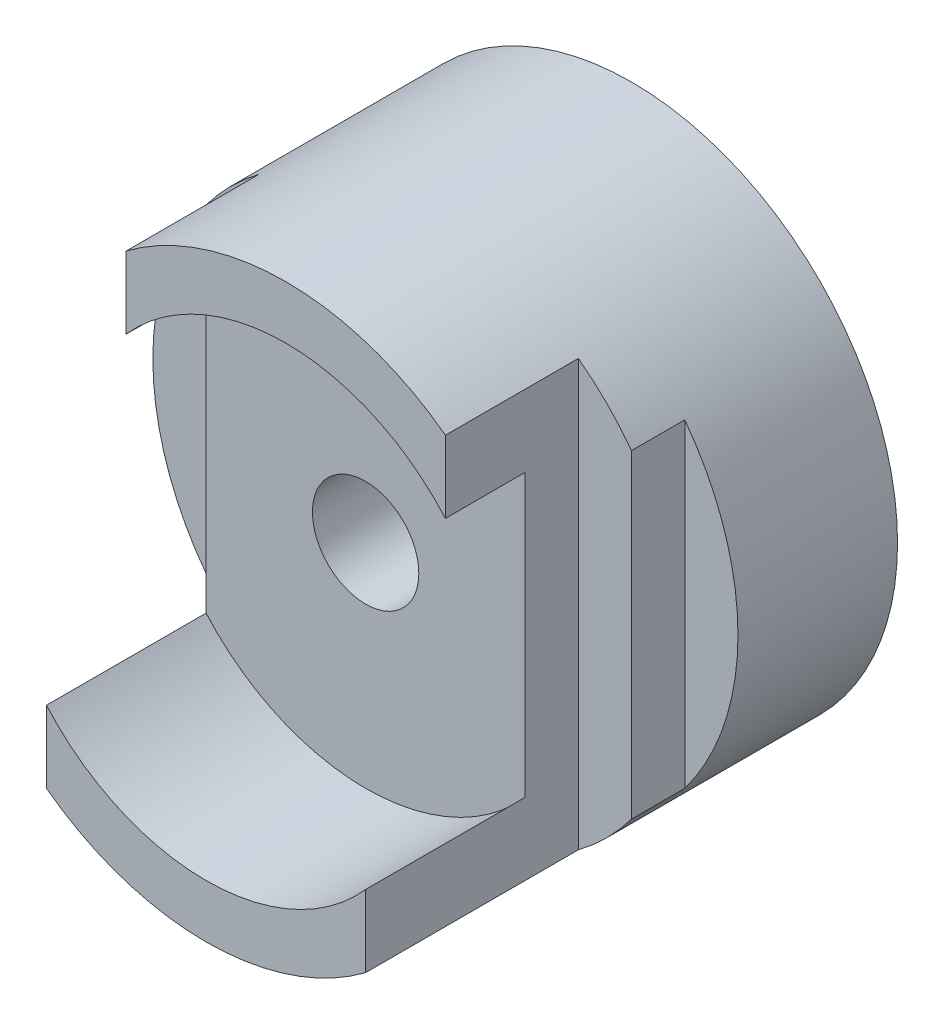
SolidWorks part; units mm, degrees
ref_plane "Front" through (0, 0, 0) normal (0, 0, 1) x (1, 0, 0)
ref_plane "Top" through (0, 0, 0) normal (0, 1, 0) x (1, 0, 0)
ref_plane "Right" through (0, 0, 0) normal (1, 0, 0) x (0, 0, -1)
sketch "Sketch2" plane through (0, 0, 0) normal (0, 0, 1) x (1, 0, 0)
  circle A0 centre (0, 0) radius 5
  circle A1 centre (0, 0) radius 1
  dimension "D1" = 2
  dimension "D2" = 10
extrude "Boss-Extrude1" add sketch "Sketch2" along normal blind 8
sketch "Sketch3" plane through (0, 0, 0) normal (0, 1, 0) x (1, 0, 0)
  line L0 (5, 0) -> (-5, 0) construction
  line L1 (-5, 0) -> (-4, 0)
  line L2 (-5, 0) -> (-5, -1)
  line L3 (-5, -1) -> (-4, -1)
  line L4 (-4, 0) -> (-4, -1)
  line L6 (5, -8) -> (3, -8)
  line L7 (-5, -8) -> (5, -8) construction
  line L8 (3, -8) -> (3, -4)
  line L9 (3, -4) -> (4, -4)
  line L10 (4, -4) -> (4, -3)
  line L11 (4, -3) -> (5, -3)
  line L12 (5, -8) -> (5, 0) construction
  line L13 (5, -3) -> (5, -8)
  line L15 (-5, -8) -> (-3, -8)
  line L16 (-5, -8) -> (-5, -4)
  line L17 (-5, -4) -> (-3, -4)
  line L18 (-3, -8) -> (-3, -4)
  dimension "D1" = 1
  dimension "D2" = 1
  dimension "D3" = 2
  dimension "D4" = 4
  dimension "D5" = 4
  dimension "D6" = 1
  dimension "D7" = 1
  dimension "D8" = 1
extrude "Cut-Extrude1" cut sketch "Sketch3" against normal mid plane 8
sketch "Sketch4" plane through (0, 0, 8) normal (0, 0, 1) x (1, 0, 0)
  circle A0 centre (0, 0) radius 4
  arc A1 (3, 4) -> (-3, 4) centre (0, 0) ccw construction
  dimension "D1" = 1
extrude "Cut-Extrude2" cut sketch "Sketch4" against normal blind 3
sketch "Sketch5" plane through (0, 0, 8) normal (0, 0, 1) x (1, 0, 0)
  line L1 (-4.0413, 1.2394) -> (5.3288, 1.2394)
  line L2 (-4.0413, 1.2394) -> (-4.0413, 6.2729)
  line L3 (-4.0413, 6.2729) -> (5.3288, 6.2729)
  line L4 (5.3288, 1.2394) -> (5.3288, 6.2729)
extrude "Cut-Extrude3" cut sketch "Sketch5" against normal blind 1.5
